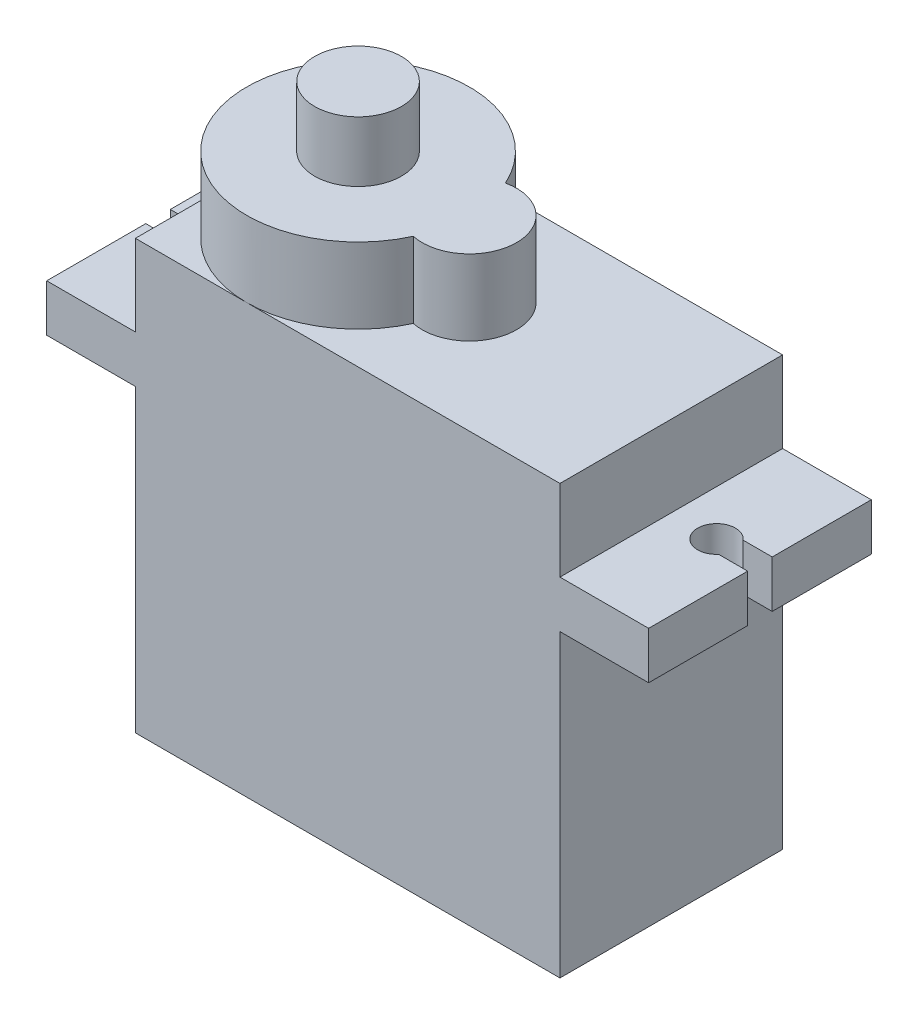
SolidWorks part; units mm, degrees
ref_plane "Front Plane" through (0, 0, 0) normal (0, 0, 1) x (1, 0, 0)
ref_plane "Top Plane" through (0, 0, 0) normal (0, 1, 0) x (1, 0, 0)
ref_plane "Right Plane" through (0, 0, 0) normal (1, 0, 0) x (0, 0, -1)
sketch "Sketch2" plane through (0, 0, 0) normal (0, 0, 1) x (1, 0, 0)
  line L0 (0, 0) -> (22.5, 0)
  line L1 (22.5, 0) -> (22.5, 15.9)
  line L2 (22.5, 15.9) -> (27.2, 15.9)
  line L3 (27.2, 15.9) -> (27.2, 18.4)
  line L4 (27.2, 18.4) -> (22.5, 18.4)
  line L5 (22.5, 18.4) -> (22.5, 22.7)
  line L6 (22.5, 22.7) -> (0, 22.7)
  line L7 (0, 22.7) -> (0, 18.4)
  line L8 (0, 18.4) -> (-4.7, 18.4)
  line L9 (-4.7, 18.4) -> (-4.7, 15.9)
  line L10 (-4.7, 15.9) -> (0, 15.9)
  line L11 (0, 15.9) -> (0, 0)
  dimension "D1" = 15.9
  dimension "D2" = 2.5
  dimension "D3" = 22.5
  dimension "D4" = 4.7
  dimension "D5" = 22.5
extrude "Boss-Extrude1" add sketch "Sketch2" along normal blind 11.8
sketch "Sketch3" plane through (0, 22.7, 0) normal (0, 1, 0) x (1, 0, 0)
  arc A0 (11.2703, -3.4568) -> (11.2703, -8.3432) centre (5.9, -5.9) ccw
  arc A1 (11.2703, -8.3432) -> (11.2703, -3.4568) centre (11.8, -5.9) ccw
  dimension "D1" = 11.8
extrude "Boss-Extrude2" add sketch "Sketch3" along normal blind 4
sketch "Sketch4" plane through (0, 26.7, 0) normal (0, 1, 0) x (1, 0, 0)
  circle A1 centre (5.9, -5.9) radius 2.3
extrude "Boss-Extrude3" add sketch "Sketch4" along normal blind 3.2
sketch "Sketch5" plane through (0, 18.4, 0) normal (0, 1, 0) x (1, 0, 0)
  line L1 (27.2, -11.8) -> (27.2, 0) construction
  line L2 (27.2, -5.9) -> (27.2, -5.25)
  line L3 (27.2, -5.9) -> (27.2, -6.55)
  line L4 (27.2, -5.25) -> (25.6599, -5.25)
  line L5 (27.2, -6.55) -> (25.6599, -6.55)
  arc A0 (25.6599, -5.25) -> (25.6599, -6.55) centre (24.9, -5.9) ccw
extrude "Cut-Extrude1" cut sketch "Sketch5" against normal blind 3.2
sketch "Sketch6" plane through (0, 18.4, 0) normal (0, 1, 0) x (1, 0, 0)
  line L1 (-4.7, -11.8) -> (-4.7, 0) construction
  line L2 (-4.7, -5.9) -> (-4.7, -5.25)
  line L3 (-4.7, -5.9) -> (-4.7, -6.55)
  line L4 (-4.7, -6.55) -> (-3.1599, -6.55)
  line L5 (-4.7, -5.25) -> (-3.1599, -5.25)
  arc A0 (-3.1599, -6.55) -> (-3.1599, -5.25) centre (-2.4, -5.9) ccw
extrude "Cut-Extrude2" cut sketch "Sketch6" against normal blind 3.2
